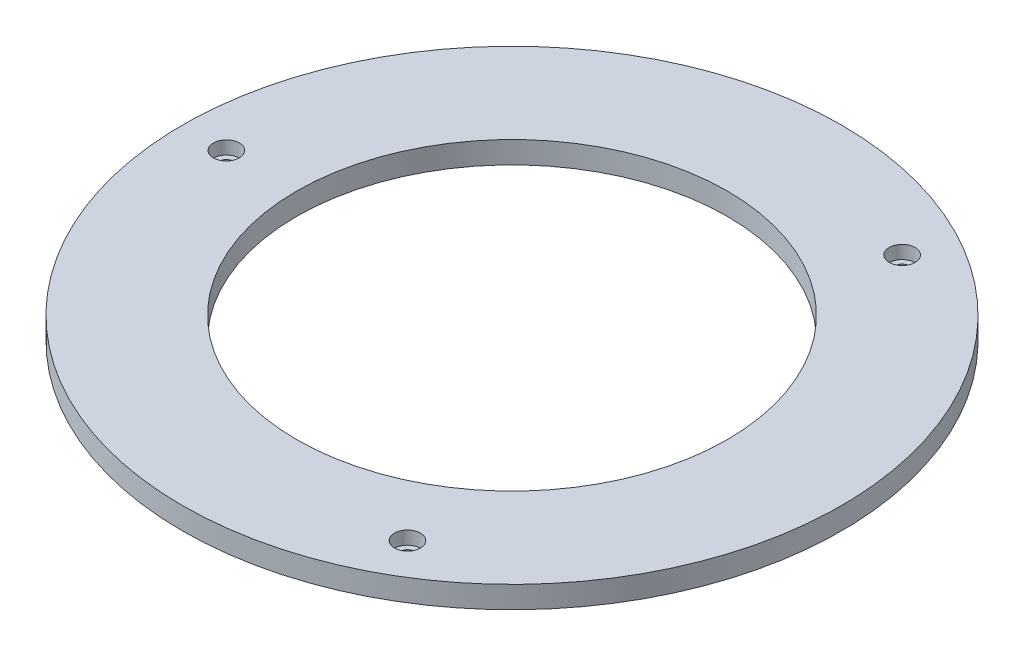
SolidWorks part; units mm, degrees
material "PLA"
ref_plane "Alzado" through (0, 0, 0) normal (0, 0, 1) x (1, 0, 0)
ref_plane "Planta" through (0, 0, 0) normal (0, 1, 0) x (1, 0, 0)
ref_plane "Vista lateral" through (0, 0, 0) normal (1, 0, 0) x (0, 0, -1)
sketch "Croquis1" plane through (0, 0, 0) normal (0, 1, 0) x (1, 0, 0)
  circle A0 centre (0, 0) radius 75
  circle A1 centre (0, 0) radius 49
  dimension "D1" = 98
  dimension "D2" = 150
extrude "Saliente-Extruir1" add sketch "Croquis1" along normal blind 5
sketch "Croquis2" plane through (0, 5, 0) normal (0, 1, 0) x (1, 0, 0)
  circle A0 centre (-65, 0) radius 1.7
  dimension "D1" = 3.4
  dimension "D2" = 65
extrude "Cortar-Extruir1" cut sketch "Croquis2" against normal blind 5
sketch "Croquis3" plane through (0, 5, 0) normal (0, 1, 0) x (1, 0, 0)
  circle A0 centre (-65, 0) radius 2.95
  dimension "D1" = 5.9
extrude "Cortar-Extruir2" cut sketch "Croquis3" against normal blind 3
pattern_circular "MatrizC1" count 3 over 360 about axis through (0, 0, 0) along (0, 1, 0) of "Cortar-Extruir2", "Cortar-Extruir1"
